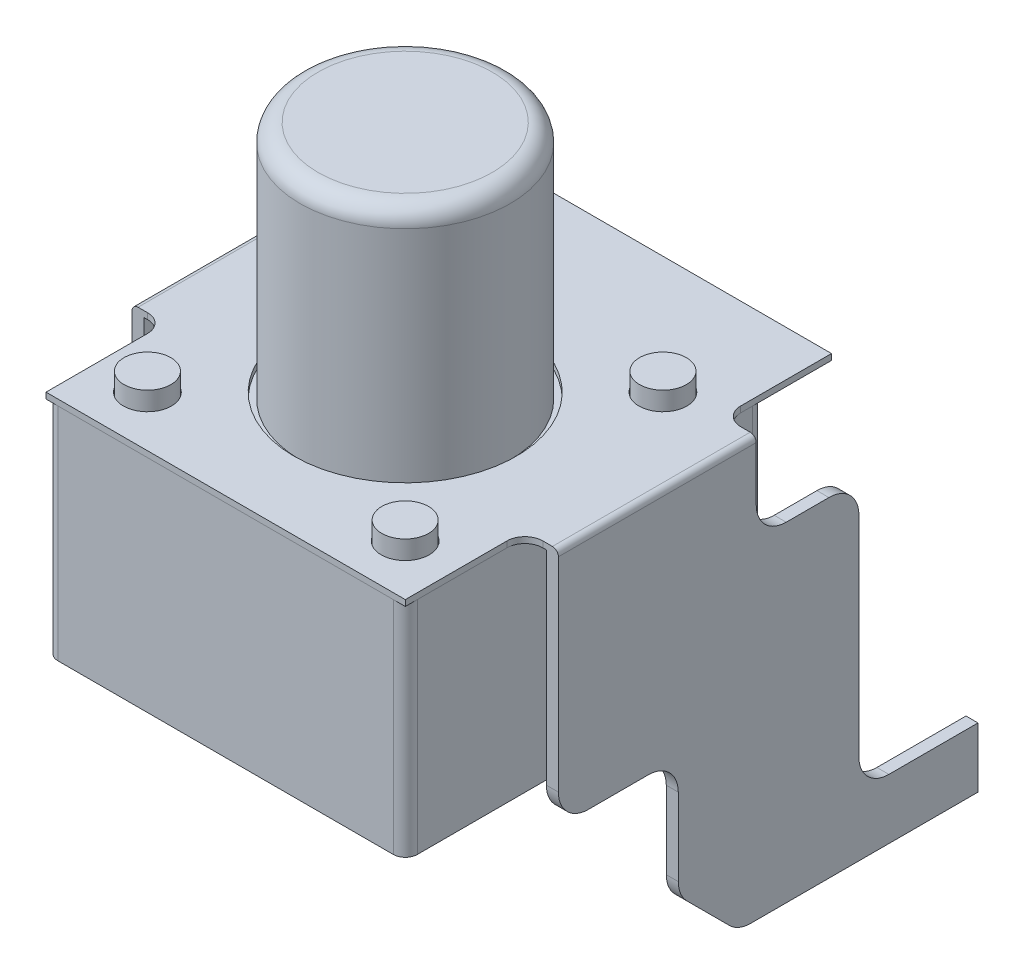
SolidWorks part; units mm, degrees
ref_plane "Front Plane" through (0, 0, 0) normal (0, 0, 1) x (1, 0, 0)
ref_plane "Top Plane" through (0, 0, 0) normal (0, 1, 0) x (1, 0, 0)
ref_plane "Right Plane" through (0, 0, 0) normal (1, 0, 0) x (0, 0, -1)
sketch "Sketch4" plane through (0, 0, 0) normal (1, 0, 0) x (0, 0, -1)
  line L0 (2.3, 0.1) -> (-1, 0.1)
  line L1 (-1, 0.1) -> (-1, -3.9)
  line L2 (-1, -3.9) -> (1, -3.9)
  line L3 (1, -3.9) -> (1, -5.9)
  line L4 (1, -5.9) -> (2, -6.9)
  line L5 (2, -6.9) -> (6, -6.9)
  line L6 (4.0132, -5.9) -> (4.0132, -1.4)
  line L7 (4.0132, -1.4) -> (2.3, -1.4)
  line L8 (2.3, -1.4) -> (2.3, 0.1)
  line L9 (4.0132, -5.9) -> (6, -5.9)
  line L10 (6, -5.9) -> (6, -6.9)
  point P6 (1, -6.9)
  dimension "D1" = 7
  dimension "D2" = 4
  dimension "D3" = 7
  dimension "D4" = 4.0132
  dimension "D5" = 1.5
  dimension "D6" = 3.3
  dimension "D7" = 1
  dimension "D8" = 2
  dimension "D9" = 1
  dimension "D10" = 0.1
sketch "Sketch1" plane through (0, 0, 0) normal (0, 1, 0) x (1, 0, 0)
  line L0 (-2.9972, 2.995) -> (2.9972, -2.995) construction
  line L1 (-2.9972, 2.995) -> (2.9972, 2.995)
  line L2 (-2.9972, 2.995) -> (-2.9972, -2.995)
  line L3 (-2.9972, -2.995) -> (2.9972, -2.995)
  line L4 (2.9972, 2.995) -> (2.9972, -2.995)
  dimension "D1" = 5.9944
  dimension "D2" = 5.99
extrude "Extrude1" add sketch "Sketch1" against normal blind 3.683
sketch "Sketch2" plane through (0, 0, 0) normal (0, 1, 0) x (1, 0, 0)
  circle A0 centre (0, 0) radius 1.7526
  dimension "D1" = 3.5052
sketch "Sketch7" plane through (0, 0, 0) normal (0, 1, 0) x (1, 0, 0)
  line L0 (-3.556, 0) -> (3.556, 0) construction
  line L1 (-3.556, 2.3) -> (-2.9972, 2.3)
  line L2 (-3.556, 2.3) -> (-3.556, -1)
  line L3 (-3.556, -1) -> (-2.9972, -1)
  line L4 (2.9972, 2.995) -> (-2.9972, 2.995)
  line L5 (2.9972, -2.995) -> (2.9972, 2.995)
  line L6 (-2.9972, -2.995) -> (2.9972, -2.995)
  line L7 (-2.9972, 2.995) -> (-2.9972, -2.995)
  line L8 (2.9972, 2.995) -> (-2.9972, 2.995)
  line L9 (2.9972, -2.995) -> (2.9972, -1)
  line L10 (-2.9972, -2.995) -> (2.9972, -2.995)
  line L11 (-2.9972, 2.995) -> (-2.9972, 2.3)
  line L12 (3.556, 2.3) -> (3.556, -1)
  line L13 (-2.9972, -1) -> (-2.9972, -2.995)
  line L14 (2.9972, 2.3) -> (3.556, 2.3)
  line L15 (2.9972, -1) -> (3.556, -1)
  line L16 (2.9972, 2.3) -> (2.9972, 2.995)
  line L17 (-2.9972, 2.3) -> (2.9972, 2.3) construction
  line L18 (-2.9972, -1) -> (2.9972, -1) construction
  dimension "D2" = 7.112
  dimension "D1" = 0
ref_plane "Plane2" through (3.556, 0, 0) normal (1, 0, 0) x (0, 0, -1)
sketch "Sketch5" plane through (3.556, 0, 0) normal (1, 0, 0) x (0, 0, -1)
  line L11 (2.3, 0.1) -> (-1, 0.1)
  line L12 (-1, 0.1) -> (-1, -3.9)
  line L13 (-1, -3.9) -> (1, -3.9)
  line L14 (1, -3.9) -> (1, -5.9)
  line L15 (1, -5.9) -> (2, -6.9)
  line L16 (2, -6.9) -> (6, -6.9)
  line L17 (6, -6.9) -> (6, -5.9)
  line L18 (6, -5.9) -> (4.0132, -5.9)
  line L19 (4.0132, -5.9) -> (4.0132, -1.4)
  line L20 (4.0132, -1.4) -> (2.3, -1.4)
  line L21 (2.3, -1.4) -> (2.3, 0.1)
  line L22 (2.3, 0.1) -> (-1, 0.1)
  line L23 (-1, 0.1) -> (-1, -3.9)
  line L24 (-1, -3.9) -> (1, -3.9)
  line L25 (1, -3.9) -> (1, -5.9)
  line L26 (1, -5.9) -> (2, -6.9)
  line L27 (2, -6.9) -> (6, -6.9)
  line L28 (6, -6.9) -> (6, -5.9)
  line L29 (6, -5.9) -> (4.0132, -5.9)
  line L30 (4.0132, -5.9) -> (4.0132, -1.4)
  line L31 (4.0132, -1.4) -> (2.3, -1.4)
  line L32 (2.3, -1.4) -> (2.3, 0.1)
  dimension "D1" = 0
extrude "Extrude2" add sketch "Sketch5" against normal blind 0.2 separate body contours L25 L26 L27 L28 L29 L30 L31 L32 L22 L23 L24
fillet "Fillet3" radius 0.5 7 edges at (3.456, -1.4, -2.3) (3.456, -1.4, -4.0132) (3.456, -5.9, -4.0132) (3.456, -6.9, -2) (3.456, -5.9, -1) (3.456, -3.9, -1) (3.456, -3.9, 1)
mirror "Mirror1" about plane through (0, 0, 0) normal (1, 0, 0) of bodies 102
sketch "Sketch6" plane through (0, 0, 0) normal (0, 1, 0) x (1, 0, 0)
  line L0 (-2.15, 2.15) -> (2.15, -2.15) construction
  line L1 (-2.15, 2.15) -> (2.15, 2.15) construction
  line L2 (-2.15, 2.15) -> (-2.15, -2.15) construction
  line L3 (-2.15, -2.15) -> (2.15, -2.15) construction
  line L4 (2.15, 2.15) -> (2.15, -2.15) construction
  line L12 (2.9972, -1) -> (3.556, -1)
  line L13 (3.556, -1) -> (3.556, 2.3)
  line L14 (3.556, 2.3) -> (2.9972, 2.3)
  line L15 (2.9972, 2.3) -> (2.9972, 2.995)
  line L16 (2.9972, 2.995) -> (-2.9972, 2.995)
  line L17 (-2.9972, 2.995) -> (-2.9972, 2.3)
  line L18 (-2.9972, 2.3) -> (-3.556, 2.3)
  line L19 (-3.556, 2.3) -> (-3.556, -1)
  line L20 (-3.556, -1) -> (-2.9972, -1)
  line L21 (-2.9972, -1) -> (-2.9972, -2.995)
  line L22 (-2.9972, -2.995) -> (2.9972, -2.995)
  line L23 (2.9972, -2.995) -> (2.9972, -1)
  line L24 (3.2972, -1) -> (3.556, -1)
  line L25 (3.556, -1) -> (3.556, 2.3)
  line L26 (3.556, 2.3) -> (3.2972, 2.3)
  line L27 (2.9972, 2.6) -> (2.9972, 4.115)
  line L28 (2.9972, 4.115) -> (-2.9972, 4.115)
  line L29 (-2.9972, 4.115) -> (-2.9972, 2.6)
  line L30 (-3.2972, 2.3) -> (-3.556, 2.3)
  line L31 (-3.556, 2.3) -> (-3.556, -1)
  line L32 (-3.556, -1) -> (-3.2972, -1)
  line L33 (-2.9972, -1.3) -> (-2.9972, -2.995)
  line L34 (-2.9972, -2.995) -> (2.9972, -2.995)
  line L35 (2.9972, -2.995) -> (2.9972, -1.3)
  circle A0 centre (0, 0) radius 1.8526
  circle A1 centre (0, 0) radius 1.7526 construction
  arc A2 (3.2972, 2.3) -> (2.9972, 2.6) centre (3.2972, 2.6) cw
  arc A3 (3.2972, -1) -> (2.9972, -1.3) centre (3.2972, -1.3) ccw
  arc A4 (-2.9972, 2.6) -> (-3.2972, 2.3) centre (-3.2972, 2.6) cw
  arc A5 (-3.2972, -1) -> (-2.9972, -1.3) centre (-3.2972, -1.3) cw
  circle A6 centre (-2.15, 2.15) radius 0.4
  circle A7 centre (2.15, 2.15) radius 0.4
  circle A8 centre (2.15, -2.15) radius 0.4
  circle A9 centre (-2.15, -2.15) radius 0.4
  dimension "D1" = 0.1
  dimension "D3" = 0.3
  dimension "D5" = 0.8
  dimension "D4" = 7.11
  dimension "D6" = 4.3
  dimension "D2" = 0
extrude "Extrude3" add sketch "Sketch6" along normal through all
extrude "Extrude4" add sketch "Sketch2" along normal blind 4 separate body contours A0
fillet "Fillet1" radius 0.1 2 edges at (3.556, 0.1, -0.65) (-3.556, 0.1, -0.65)
ref_plane "Plane1" through (0, 0, -4.01) normal (0, 0, 1) x (1, 0, 0)
sketch "Sketch8" plane through (0, 0, 0) normal (0, 1, 0) x (1, 0, 0)
  circle A1 centre (2.15, 2.15) radius 0.39
  circle A2 centre (2.15, -2.15) radius 0.39
  circle A3 centre (-2.15, 2.15) radius 0.39
  circle A4 centre (-2.15, -2.15) radius 0.39
  circle A5 centre (-2.15, 2.15) radius 0.4 construction
  dimension "D1" = 0.01
extrude "Boss-Extrude1" add sketch "Sketch8" along normal offset from surface (0.4048 mm away) 0.3048 up to face at (0, 0.1, -0.6275) offset beyond the face yes
fillet "Fillet4" radius 0.2 4 edges at (-2.9972, -1.8415, -2.995) (2.9972, -1.8415, -2.995) (2.9972, -1.8415, 2.995) (-2.9972, -1.8415, 2.995)
fillet "Fillet5" radius 0.3 1 edges at (0, 4, 1.7526)
